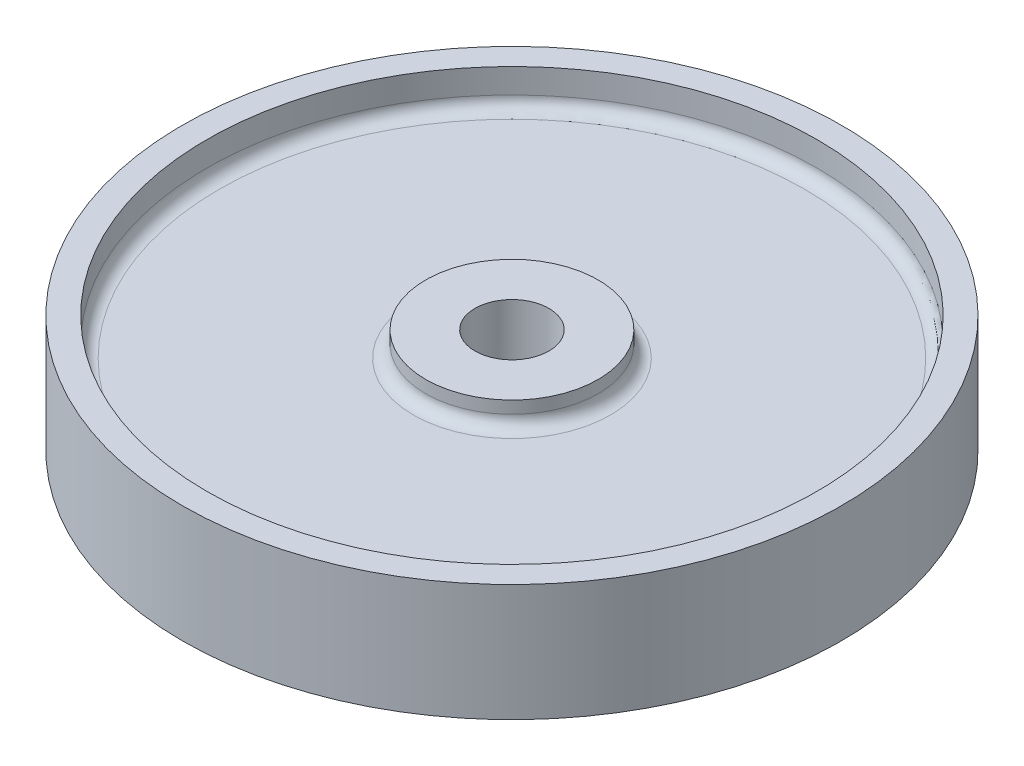
SolidWorks part; units mm, degrees
ref_plane "Front Plane" through (0, 0, 0) normal (0, 0, 1) x (1, 0, 0)
ref_plane "Top Plane" through (0, 0, 0) normal (0, 1, 0) x (1, 0, 0)
ref_plane "Right Plane" through (0, 0, 0) normal (1, 0, 0) x (0, 0, -1)
sketch "Sketch1" plane through (0, 0, 0) normal (0, 1, 0) x (1, 0, 0)
  circle A0 centre (0, 0) radius 53.5
  dimension "D1" = 107
extrude "Boss-Extrude1" add sketch "Sketch1" along normal blind 19
sketch "Sketch2" plane through (0, 19, 0) normal (0, 1, 0) x (1, 0, 0)
  circle A0 centre (0, 0) radius 49.5
  circle A1 centre (0, 0) radius 53.5 construction
  dimension "D1" = 4
extrude "Cut-Extrude1" cut sketch "Sketch2" against normal blind 6
fillet "Fillet1" radius 2 1 edges at (0, 13, 49.5)
sketch "Sketch3" plane through (0, 13, 0) normal (0, 1, 0) x (1, 0, 0)
  circle A0 centre (0, 0) radius 14
  dimension "D1" = 28
extrude "Boss-Extrude2" add sketch "Sketch3" along normal blind 4
fillet "Fillet2" radius 2 1 edges at (0, 13, 14)
ref_plane "Plane1" through (0, 9.5, 0) normal (0, 1, 0) x (1, 0, 0)
mirror "Mirror1" about plane through (0, 9.5, 0) normal (0, 1, 0) of "Fillet2", "Boss-Extrude2", "Fillet1", "Cut-Extrude1"
sketch "Sketch5" plane through (0, 17, 0) normal (0, 1, 0) x (1, 0, 0)
  circle A0 centre (0, 0) radius 6
  dimension "D1" = 12
extrude "Cut-Extrude2" cut sketch "Sketch5" against normal through all
